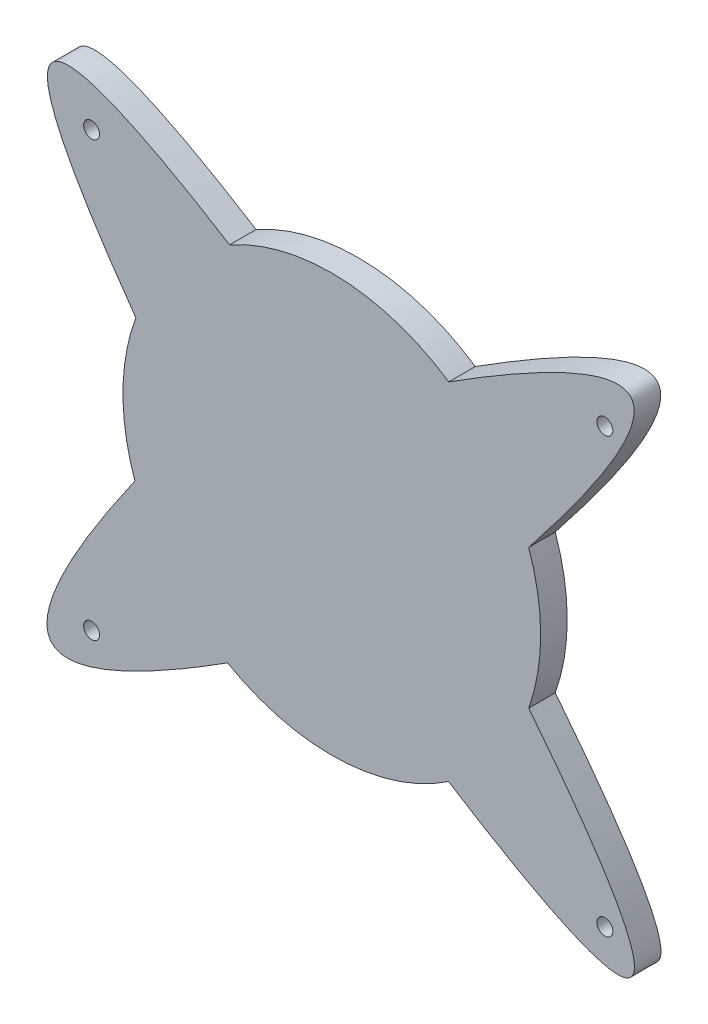
SolidWorks part; units mm, degrees
ref_plane "Front Plane" through (0, 0, 0) normal (0, 0, 1) x (1, 0, 0)
ref_plane "Top Plane" through (0, 0, 0) normal (0, 1, 0) x (1, 0, 0)
ref_plane "Right Plane" through (0, 0, 0) normal (1, 0, 0) x (0, 0, -1)
sketch "Sketch2" plane through (0, 0, 0) normal (0, 0, 1) x (1, 0, 0)
  circle A1 centre (-39, 24.5) radius 0.9
  circle A2 centre (-39, -24.5) radius 0.9
  circle A3 centre (19, -24.5) radius 0.9
  circle A4 centre (19, 24.5) radius 0.9
  arc A5 (-34.0029, 8.6045) -> (-34.1053, -7.4205) centre (-11.8548, 0.45) ccw
  arc A6 (1.3594, 20.0054) -> (-23.4078, 21.0305) centre (-11.8548, 0.45) ccw
  arc A7 (-23.6427, -19.9969) -> (1.3336, -19.1228) centre (-11.8548, 0.45) ccw
  arc A8 (10.4003, -7.4074) -> (10.3933, 8.3272) centre (-11.8548, 0.45) ccw
  spline S2 degree 2 poles (-34.0029, 8.6045) (-58.3335, 42.7586) (-23.4078, 21.0305) knots 0 0 0 1 1 1
  spline S3 degree 2 poles (10.1634, 8.0375) (38.3257, 43.4766) (1.2085, 19.9096) knots 0 0 0 1 1 1
  spline S4 degree 2 poles (10.4003, -7.4074) (38.1882, -42.4523) (1.3336, -19.1228) knots 0 0 0 1 1 1
  spline S5 degree 2 poles (-34.1053, -7.4205) (-58.2817, -42.0509) (-23.6427, -19.9969) knots 0 0 0 1 1 1
extrude "Boss-Extrude1" add sketch "Sketch2" along normal blind 3
